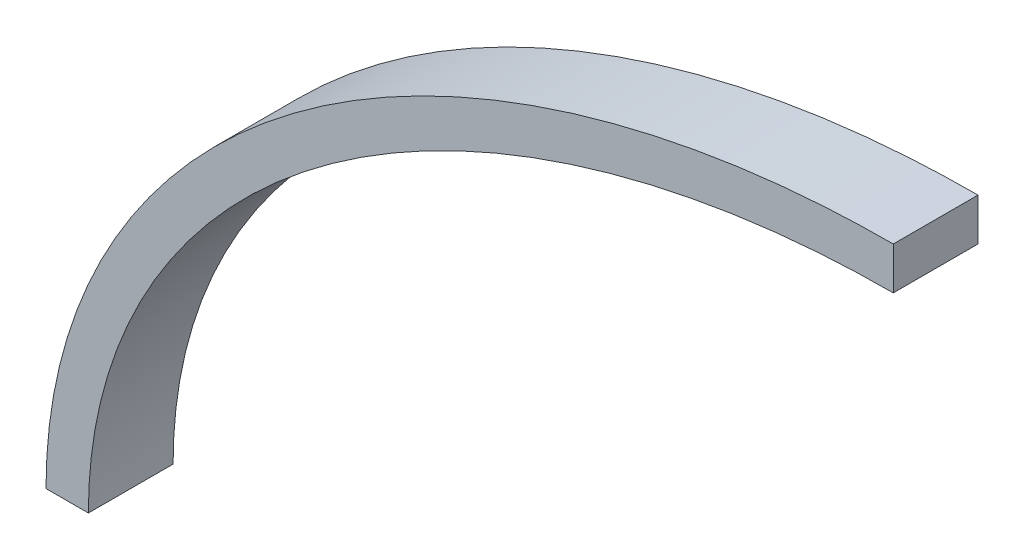
SolidWorks part; units mm, degrees
material "Balsa"
ref_plane "Alzado" through (0, 0, 0) normal (0, 0, 1) x (1, 0, 0)
ref_plane "Planta" through (0, 0, 0) normal (0, 1, 0) x (1, 0, 0)
ref_plane "Vista lateral" through (0, 0, 0) normal (1, 0, 0) x (0, 0, -1)
sketch "Sketch2" plane through (0, 0, 0) normal (0, 0, 1) x (1, 0, 0)
  line L0 (-100, 0) -> (103.1317, 0) construction
  line L1 (0, 75) -> (0, 70)
  line L2 (-100, 0) -> (-95, 0)
  ellipse E0 centre (0, 0) end of major axis (100, 0) minor radius 75 (-100, 0) -> (0, 75) cw
  spline S0 degree 1 poles (-95, 0) (0, 70) knots 0 0 1 1 construction
  spline S1 degree 3 poles (-95, 0) (-95, 4.4883) (-93.828, 13.4105) (-88.5757, 26.431) (-79.9358, 38.5697) (-68.1631, 49.3409) (-53.6761, 58.2647) (-37.0341, 64.9408) (-21.9202, 68.3805) (-9.4507, 69.7678) (-3.1466, 70) (0, 70) knots 1.570796 1.570796 1.570796 1.570796 1.767146 1.963495 2.159845 2.356194 2.552544 2.748894 2.945243 3.043418 3.141593 3.141593 3.141593 3.141593
  dimension "D1" = 5
extrude "Boss-Extrude1" add sketch "Sketch2" along normal blind 10 contours E0 L1 S1 L2
